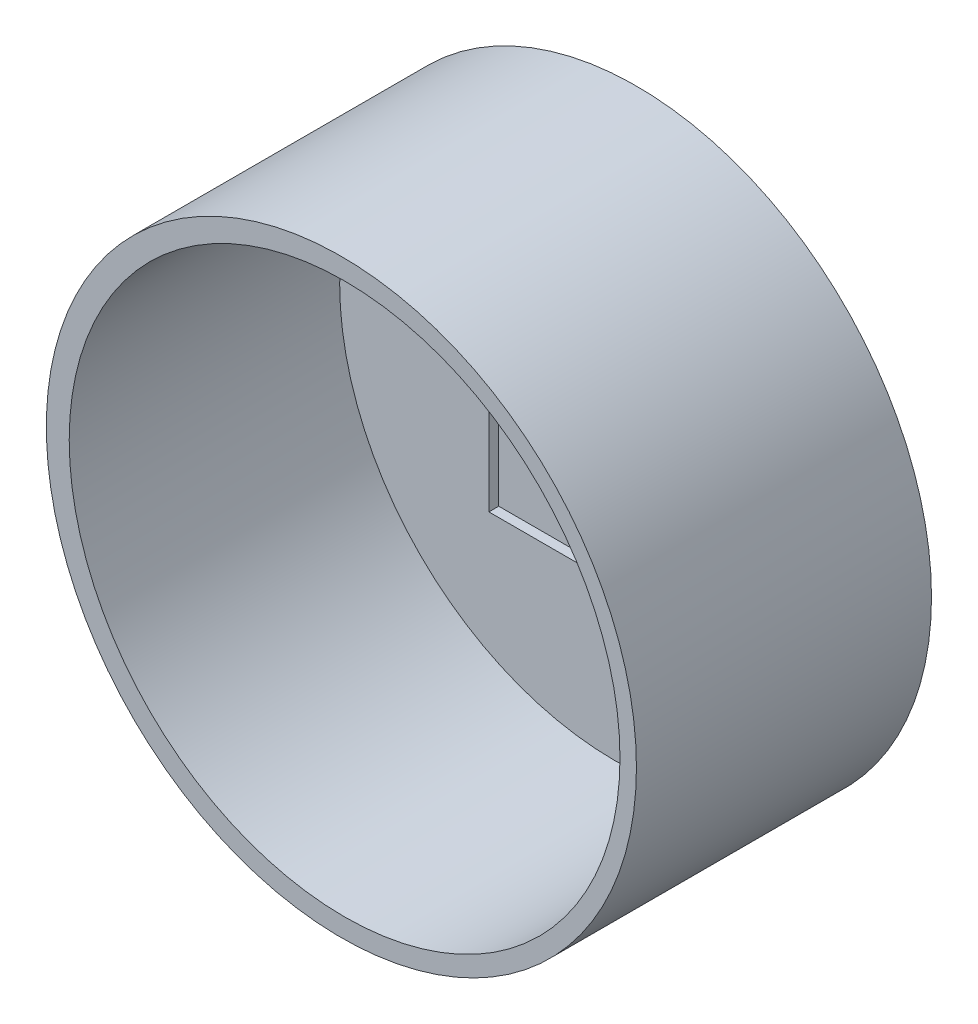
SolidWorks part; units mm, degrees
material "AISI 1020"
ref_plane "Front Plane" through (0, 0, 0) normal (0, 0, 1) x (1, 0, 0)
ref_plane "Top Plane" through (0, 0, 0) normal (0, 1, 0) x (1, 0, 0)
ref_plane "Right Plane" through (0, 0, 0) normal (1, 0, 0) x (0, 0, -1)
sketch "Sketch1" plane through (0, 0, 0) normal (0, 0, 1) x (1, 0, 0)
  circle A0 centre (0, 0) radius 76.2
  circle A1 centre (0.8288, 0) radius 71.12
  dimension "D1" = 152.4
  dimension "D2" = 142.24
extrude "Boss-Extrude1" add sketch "Sketch1" along normal blind 76.2
sketch "Sketch3" plane through (0, 0, 0) normal (0, 0, 1) x (1, 0, 0)
  circle A0 centre (0, 0) radius 76.2
extrude "Boss-Extrude2" add sketch "Sketch3" along normal blind 6.35
sketch "Sketch4" plane through (0, 0, 6.35) normal (0, 0, 1) x (1, 0, 0)
  line L1 (-31.75, 31.75) -> (31.75, 31.75)
  line L2 (-31.75, 31.75) -> (-31.75, -31.75)
  line L3 (-31.75, -31.75) -> (31.75, -31.75)
  line L4 (31.75, 31.75) -> (31.75, -31.75)
  point P5 (0, 31.75)
  point P7 (-31.75, 0)
  dimension "D1" = 63.5
  dimension "2.5" = 63.5
extrude "Cut-Extrude1" cut sketch "Sketch4" against normal blind 2.54
